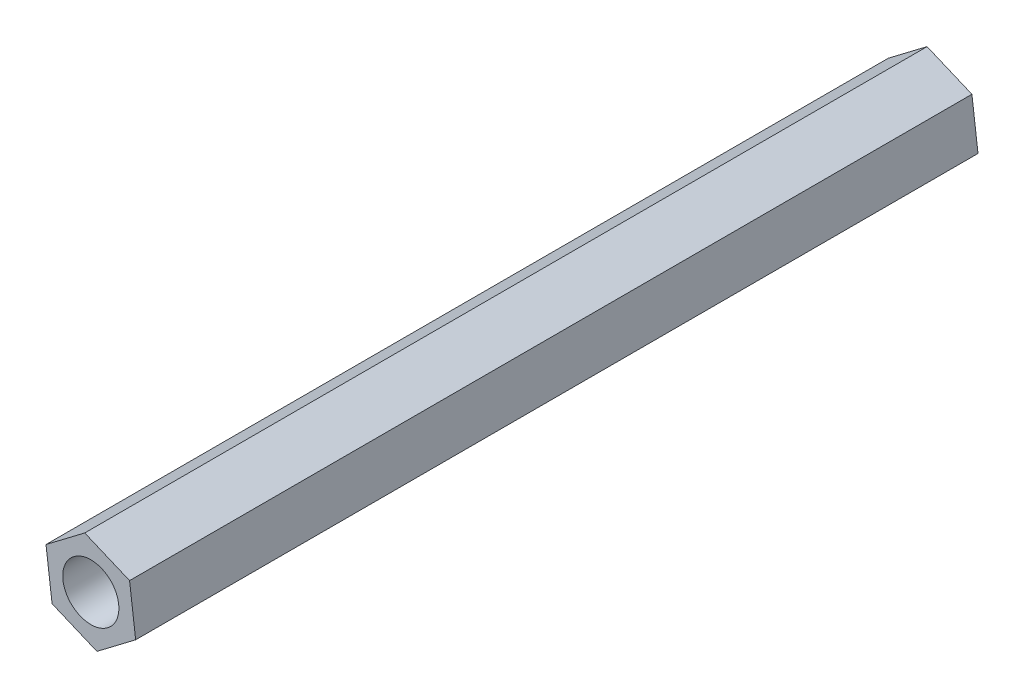
SolidWorks part; units mm, degrees
ref_plane "前视基准面" through (0, 0, 0) normal (0, 0, 1) x (1, 0, 0)
ref_plane "上视基准面" through (0, 0, 0) normal (0, 1, 0) x (1, 0, 0)
ref_plane "右视基准面" through (0, 0, 0) normal (1, 0, 0) x (0, 0, -1)
other "Configuration Table"
sketch "草图1" plane through (0, 0, 0) normal (0, 0, 1) x (1, 0, 0)
  line L1 (2.7598, 2.0937) -> (-0.4332, 3.4369)
  line L2 (-0.4332, 3.4369) -> (-3.1931, 1.3432)
  line L3 (-3.1931, 1.3432) -> (-2.7598, -2.0937)
  line L4 (-2.7598, -2.0937) -> (0.4332, -3.4369)
  line L5 (0.4332, -3.4369) -> (3.1931, -1.3432)
  line L6 (3.1931, -1.3432) -> (2.7598, 2.0937)
  circle A0 centre (0, 0) radius 3 construction
  dimension "D1" = 6
extrude "凸台-拉伸1" add sketch "草图1" along normal blind 60
sketch "草图2" plane through (0, 0, 60) normal (0, 0, 1) x (1, 0, 0)
  circle A0 centre (0, 0) radius 2
  dimension "D1" = 4
extrude "切除-拉伸1" cut sketch "草图2" against normal through all both and the other way through all
